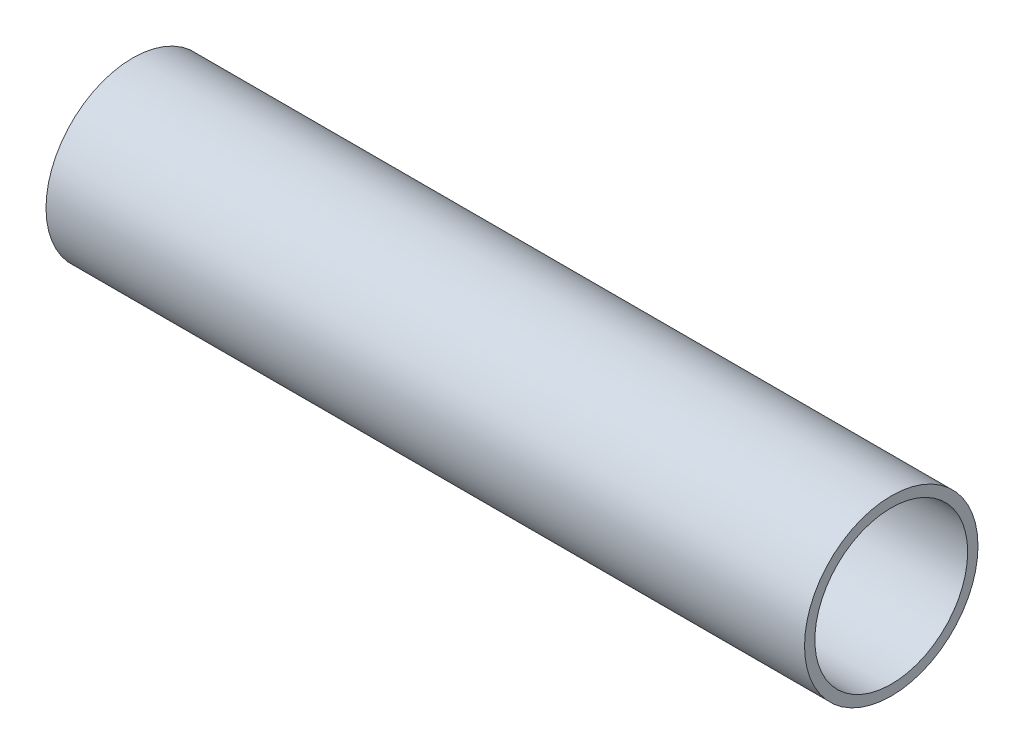
SolidWorks part; units mm, degrees
ref_plane "Front Plane" through (0, 0, 0) normal (0, 0, 1) x (1, 0, 0)
ref_plane "Top Plane" through (0, 0, 0) normal (0, 1, 0) x (1, 0, 0)
ref_plane "Right Plane" through (0, 0, 0) normal (1, 0, 0) x (0, 0, -1)
sketch "Sketch1" plane through (0, 0, 0) normal (1, 0, 0) x (0, 0, -1)
  circle A0 centre (0, 0) radius 6.3
  point P3 (0, 0)
  dimension "D1" = 12.6
extrude "Extrude-Thin1" add sketch "Sketch1" along normal blind 55.1 thin thin type one direction reverse wall 0.75
